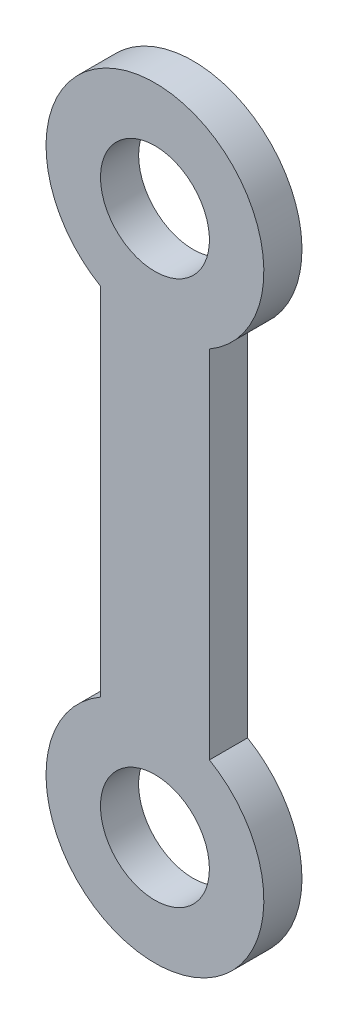
SolidWorks part; units mm, degrees
ref_plane "Front Plane" through (0, 0, 0) normal (0, 0, 1) x (1, 0, 0)
ref_plane "Top Plane" through (0, 0, 0) normal (0, 1, 0) x (1, 0, 0)
ref_plane "Right Plane" through (0, 0, 0) normal (1, 0, 0) x (0, 0, -1)
sketch "Sketch1" plane through (0, 0, 0) normal (0, 0, 1) x (1, 0, 0)
  line L0 (36.798, 101.1427) -> (103.7813, 99.6461) construction
  line L1 (0, 0) -> (0, 10) construction
  line L2 (0, 10) -> (-2, 10) construction
  line L3 (-2, 16.5359) -> (-2, 3.4641)
  line L4 (2, 16.5359) -> (2, 3.4641)
  circle A0 centre (0, 0) radius 4 construction
  circle A1 centre (0, 0) radius 2
  arc A2 (2, 3.4641) -> (-2, 3.4641) centre (0, 0) cw
  circle A3 centre (0, 20) radius 2
  arc A4 (2, 16.5359) -> (-2, 16.5359) centre (0, 20) ccw
  point P17 (2, 10)
  dimension "D2" = 4
  dimension "D3" = 2
  dimension "D1" = 67
  dimension "D4" = 4
  dimension "D5" = 10
extrude "Boss-Extrude1" add sketch "Sketch1" along normal blind 1.4
